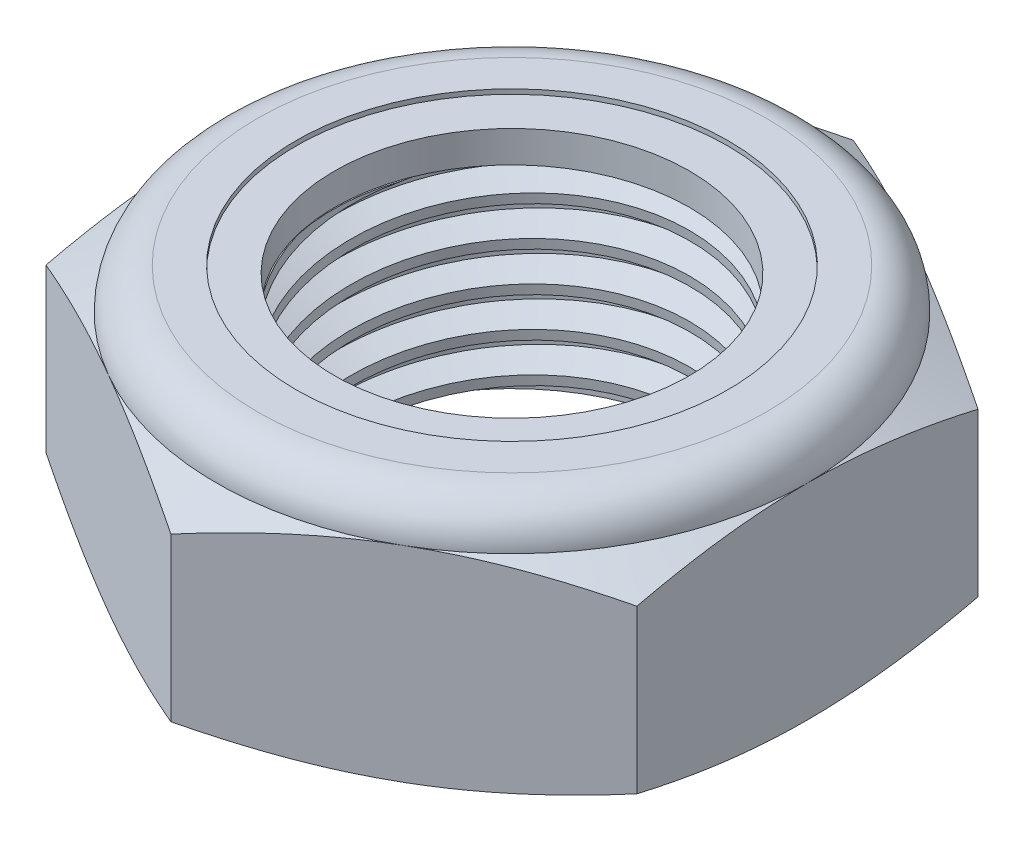
SolidWorks part; units mm, degrees
ref_plane "Front" through (0, 0, 0) normal (0, 0, 1) x (1, 0, 0)
ref_plane "Top" through (0, 0, 0) normal (0, 1, 0) x (1, 0, 0)
ref_plane "Right" through (0, 0, 0) normal (1, 0, 0) x (0, 0, -1)
sketch "Sketch1" plane through (0, 0, 0) normal (0, 1, 0) x (1, 0, 0)
  line L1 (0, 10.9985) -> (-9.525, 5.4993)
  line L2 (-9.525, 5.4993) -> (-9.525, -5.4993)
  line L3 (-9.525, -5.4993) -> (0, -10.9985)
  line L4 (0, -10.9985) -> (9.525, -5.4993)
  line L5 (9.525, -5.4993) -> (9.525, 5.4993)
  line L6 (9.525, 5.4993) -> (0, 10.9985)
  circle A0 centre (0, 0) radius 9.525 construction
  dimension "Hex Flats" = 19.05
extrude "Extrude1" add sketch "Sketch1" along normal blind 7.9375
sketch "Sketch2" plane through (0, 0, 0) normal (1, 0, 0) x (0, 0, -1)
  line L0 (-6.35, 0) -> (-6.35, 7.9375) construction
  line L1 (0, 0) -> (6.35, 0)
  line L2 (0, 0) -> (0, 7.9375)
  line L3 (0, 7.9375) -> (6.35, 7.9375)
  line L4 (6.35, 0) -> (6.35, 7.9375)
  line L5 (-5.4993, 7.9375) -> (5.4993, 7.9375) construction
  line L7 (0, -6.35) -> (0, 0) construction
  dimension "Thread Dia" = 12.7
revolve "Revolve1" add sketch "Sketch2" angle 360 about L7
sketch "Sketch3" plane through (0, 0, 0) normal (1, 0, 0) x (0, 0, -1)
  line L0 (6.35, 7.9375) -> (-6.35, 7.9375) construction
  line L1 (-6.35, 7.9375) -> (-6.35, 6.6675) construction
  line L2 (-6.35, 6.6675) -> (6.35, 7.9375) construction
  line L3 (6.35, 7.9375) -> (6.3658, 7.7795) construction
  line L4 (6.3658, 7.7795) -> (6.4764, 6.6738)
  line L5 (6.4764, 6.6738) -> (5.7529, 7.0003)
  line L6 (5.7529, 7.0003) -> (5.7213, 7.3162)
  line L7 (5.7213, 7.3162) -> (6.3658, 7.7795)
  line L8 (5.7371, 7.1583) -> (6.4211, 7.2267) construction
  line L9 (6.35, 7.9375) -> (6.35, 7.2196) construction
  line L10 (6.35, 7.2196) -> (-6.35, 5.9496) construction
  line L11 (-6.35, 5.9496) -> (-6.35, 6.6675) construction
  line L12 (-0.1353, 7.9375) -> (0.1353, 5.2316) construction
  line L13 (-6.35, 0) -> (-6.35, 7.9375) construction
  line L14 (0, 7.9375) -> (6.35, 7.9375) construction
  line L15 (6.35, 0) -> (6.35, 7.9375) construction
  point P13 (0, 6.5846)
  dimension "D1" = 0.1588
  dimension "D2" = 0.3175
  dimension "Thread Pitch" = 1.27
  dimension "D4" = 60
  dimension "D5" = 1.27
revolve "Cut-Revolve1" cut sketch "Sketch3" angle 360 about L12
pattern_linear "LPattern1" count 6 spacing 1.27 along (0, -1, 0) count 2 spacing 1.27 along (0, 1, 0) of "Cut-Revolve1"
sketch "Sketch4" plane through (0, 0, 0) normal (1, 0, 0) x (0, 0, -1)
  line L0 (0, 7.9375) -> (6.35, 7.9375)
  line L1 (6.35, 7.9375) -> (5.7213, 7.6443)
  line L2 (5.7213, 7.6443) -> (5.7213, 0.2932)
  line L3 (5.7213, 0.2932) -> (6.35, 0)
  line L4 (6.35, 0) -> (0, 0)
  line L5 (0, 0) -> (0, 7.9375)
  line L6 (6.35, 0) -> (6.35, 7.9375) construction
  line L7 (0, 7.9375) -> (6.35, 7.9375) construction
  line L8 (0, 0) -> (6.35, 0) construction
  line L9 (0, 0) -> (0, 7.9375) construction
  line L10 (0, 7.9375) -> (0, 8.6312) construction
  dimension "D1" = 25
revolve "Cut-Revolve2" cut sketch "Sketch4" angle 360 about L10
combine bodies "Combine1" operation type subtract main body 112 bodies to subtract 111
sketch "Sketch5" plane through (0, 0, 0) normal (1, 0, 0) x (0, 0, -1)
  line L0 (0, 0) -> (9.525, 0)
  line L1 (9.525, 0) -> (10.9985, 0.6871)
  line L2 (10.9985, 0.6871) -> (10.9985, 5.9275)
  line L3 (10.9985, 5.9275) -> (9.525, 6.6146)
  line L4 (8.2021, 7.9375) -> (8.2021, 9.2075)
  line L5 (8.2021, 9.2075) -> (12.2685, 9.2075)
  line L6 (12.2685, 9.2075) -> (12.2685, -1.27)
  line L7 (12.2685, -1.27) -> (0, -1.27)
  line L8 (0, -1.27) -> (0, 0)
  line L9 (9.525, 6.6146) -> (9.525, 0) construction
  line L10 (0, 0) -> (6.35, 0) construction
  line L13 (10.9985, 3.3073) -> (12.2685, 3.3073) construction
  line L14 (10.9985, 7.9375) -> (10.9985, 0) construction
  line L15 (0, 0) -> (0, 9.2075) construction
  line L20 (0, 9.2075) -> (8.2021, 9.2075) construction
  line L22 (0, 7.9375) -> (6.35, 7.9375) construction
  arc A0 (9.525, 6.6146) -> (8.2021, 7.9375) centre (8.2021, 6.6146) ccw
  dimension "D1" = 25
  dimension "D2" = 1.27
  dimension "D3" = 7.9375
  dimension "D4" = 1.3229
revolve "Cut-Revolve3" cut sketch "Sketch5" angle 360 about L15
sketch "Sketch6" plane through (0, 0, 0) normal (1, 0, 0) x (0, 0, -1)
  line L0 (0, 6.6146) -> (9.3726, 6.6146)
  line L1 (8.2021, 7.7851) -> (6.9617, 7.7851)
  line L2 (0, 9.2075) -> (0, 6.6146)
  line L3 (6.9617, 9.2075) -> (0, 9.2075)
  line L4 (0, 9.2075) -> (8.2021, 9.2075) construction
  line L5 (0, 0) -> (0, 9.2075) construction
  line L6 (0, 9.2075) -> (0, 44.323) construction
  line L7 (6.9617, 7.7851) -> (6.9617, 9.2075)
  line L8 (8.2021, 7.9375) -> (8.2021, 7.7851) construction
  line L9 (6.9617, 7.7851) -> (5.7213, 7.7851) construction
  line L10 (5.7213, 7.7851) -> (5.7213, 7.6443) construction
  arc A0 (9.3726, 6.6146) -> (8.2021, 7.7851) centre (8.2021, 6.6146) ccw
  arc A1 (9.525, 6.6146) -> (8.2021, 7.9375) centre (8.2021, 6.6146) ccw construction
  dimension "D1" = 0.1524
revolve "Cut-Revolve4" cut sketch "Sketch6" angle 360 about L6
sketch "Sketch7" plane through (0, 0, 0) normal (1, 0, 0) x (0, 0, -1)
  line L0 (5.7213, 6.6908) -> (9.2937, 6.6908)
  line L1 (8.2021, 7.7089) -> (5.7213, 7.7089)
  line L2 (5.7213, 7.7089) -> (5.7213, 6.6908)
  line L3 (5.7213, 6.6908) -> (0, 6.6908) construction
  line L4 (0, 6.6908) -> (0, 7.7089) construction
  line L5 (0, 7.7089) -> (5.7213, 7.7089) construction
  line L6 (5.7213, 6.6908) -> (5.7213, 6.6146) construction
  line L7 (0, 6.6146) -> (9.3726, 6.6146) construction
  line L8 (8.2021, 7.7089) -> (8.2021, 7.7851) construction
  arc A0 (9.2937, 6.6908) -> (8.2021, 7.7089) centre (8.2021, 6.6146) ccw
  arc A2 (9.3726, 6.6146) -> (8.2021, 7.7851) centre (8.2021, 6.6146) ccw construction
  dimension "D1" = 0.0762
revolve "Revolve2" add sketch "Sketch7" angle 360 about L4
equation "\"D1@Sketch3\"=\"Thread Pitch@Sketch3\"/8"
equation "\"D2@Sketch3\"=\"Thread Pitch@Sketch3\"/4"
equation "\"D5@Sketch3\"=\"Thread Pitch@Sketch3\""
equation "\"D4@LPattern1\"=\"Thread Pitch@Sketch3\""
equation "\"D3@LPattern1\"=\"Thread Pitch@Sketch3\""
equation "\"D1@LPattern1\"=\"Height@Extrude1\"/\"Thread Pitch@Sketch3\""
equation "\"D4@Sketch5\"=\"Height@Extrude1\"/6"
